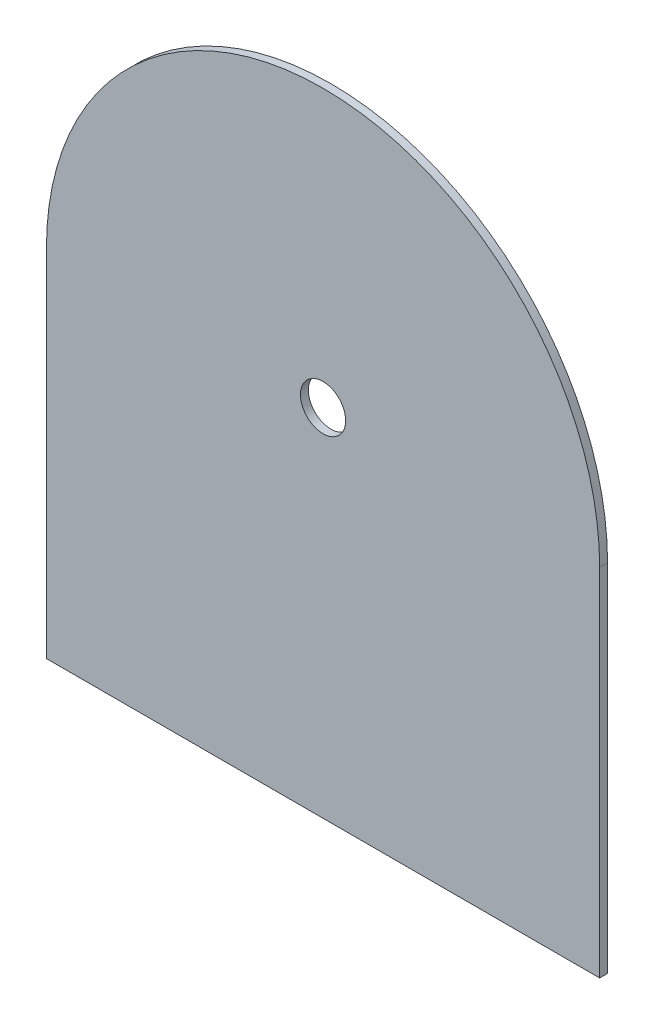
SolidWorks part; units mm, degrees
material "201 Annealed Stainless Steel (SS)"
ref_plane "Front Plane" through (0, 0, 0) normal (0, 0, 1) x (1, 0, 0)
ref_plane "Top Plane" through (0, 0, 0) normal (0, 1, 0) x (1, 0, 0)
ref_plane "Right Plane" through (0, 0, 0) normal (1, 0, 0) x (0, 0, -1)
sketch "Plate shape" plane through (0, 0, 0) normal (0, 0, 1) x (1, 0, 0)
  line L3 (0, 50) -> (175, 50) construction
  line L4 (0, 225) -> (-175, 225) construction
  line L5 (0, 225) -> (175, 225) construction
  line L7 (-175, 225) -> (-175, 0)
  line L8 (-175, 0) -> (175, 0)
  line L9 (0, 225) -> (0, 0) construction
  line L10 (175, 225) -> (175, 0)
  arc A0 (-175, 225) -> (175, 225) centre (0, 225) cw
  arc A1 (175, 225) -> (-175, 225) centre (0, 225) cw construction
  point P4 (0, 0)
  dimension "D1" = 175
  dimension "D2" = 50
  dimension "D3" = 350
extrude "Outer casing" add sketch "Plate shape" along normal blind 5
sketch "Sketch1" plane through (0, 0, 5) normal (0, 0, 1) x (1, 0, 0)
  circle A0 centre (0, 225) radius 175 construction
  arc A1 (175, 225) -> (-175, 225) centre (0, 225) ccw construction
  circle A2 centre (0, 225) radius 14.3
  dimension "D1" = 28.6
extrude "Inner Cutout" cut sketch "Sketch1" against normal blind 10
sketch "Sketch2" plane through (0, 0, 0) normal (1, 0, 0) x (0, 0, -1)
  line L0 (-5, 210.7) -> (0, 210.7) construction
  point P3 (-2.5, 210.7)
  point P4 (-2.5, 210.7)
ref_plane "Plane1" through (0, 0, 2.5) normal (0, 0, 1) x (1, 0, 0)
sketch "Sketch3" plane through (0, 0, 2.5) normal (0, 0, 1) x (1, 0, 0)
  circle A0 centre (0, 225) radius 14.3 construction
  circle A1 centre (0, 225) radius 14.3 construction
